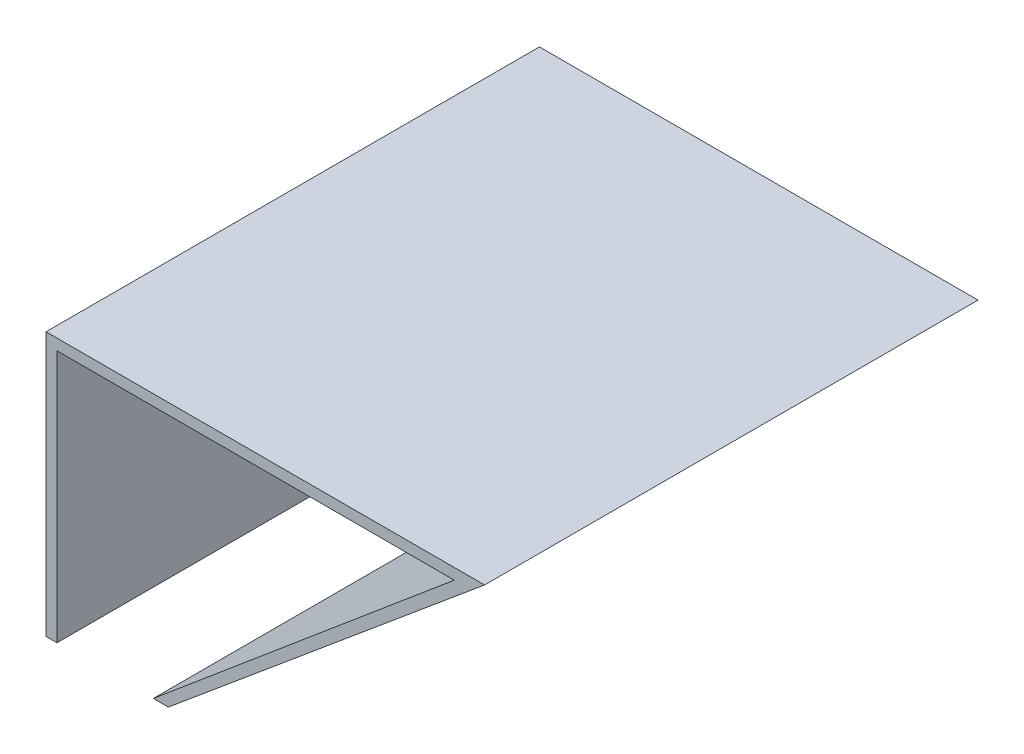
SolidWorks part; units mm, degrees
ref_plane "Front Plane" through (0, 0, 0) normal (0, 0, 1) x (1, 0, 0)
ref_plane "Top Plane" through (0, 0, 0) normal (0, 1, 0) x (1, 0, 0)
ref_plane "Right Plane" through (0, 0, 0) normal (1, 0, 0) x (0, 0, -1)
sketch "Sketch1" plane through (0, 0, 0) normal (0, 0, 1) x (1, 0, 0)
  line L1 (11.1602, 0) -> (40, 24.066)
  line L2 (40, 24.066) -> (0, 24.066)
  line L3 (0, 24.066) -> (0, 0)
  line L4 (1, 23.066) -> (1, 0)
  line L6 (9.7882, 0) -> (37.2408, 23.066)
  line L7 (37.2408, 23.066) -> (1, 23.066)
  line L10 (0, 0) -> (1, 0)
  line L11 (9.7882, 0) -> (11.1602, 0)
  dimension "D2" = 40
  dimension "D1" = 1
  dimension "D3" = 1
extrude "Boss-Extrude1" add sketch "Sketch1" along normal blind 45
